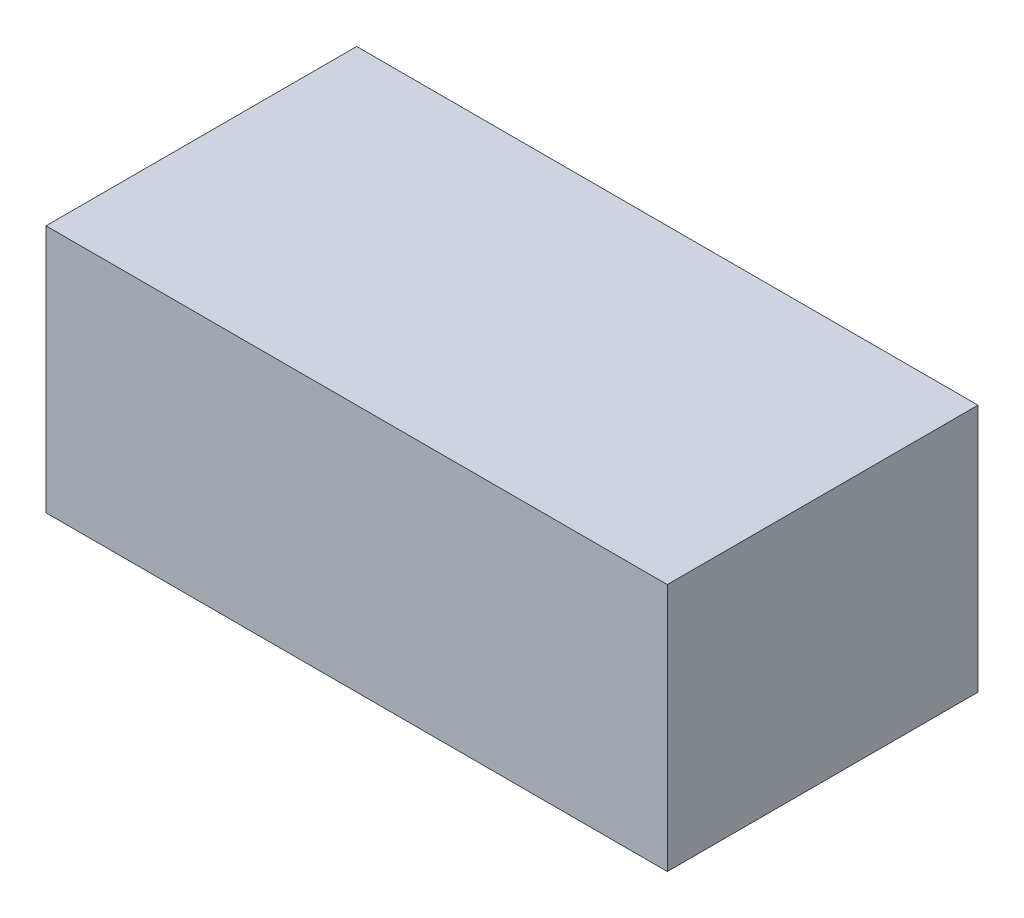
SolidWorks part; units mm, degrees
ref_plane "Front Plane" through (0, 0, 0) normal (0, 0, 1) x (1, 0, 0)
ref_plane "Top Plane" through (0, 0, 0) normal (0, 1, 0) x (1, 0, 0)
ref_plane "Right Plane" through (0, 0, 0) normal (1, 0, 0) x (0, 0, -1)
sketch "Sketch1" plane through (0, 0, 0) normal (0, 1, 0) x (1, 0, 0)
  line L1 (0, 0) -> (20, 0)
  line L2 (0, 0) -> (0, 10)
  line L3 (0, 10) -> (20, 10)
  line L4 (20, 0) -> (20, 10)
  dimension "D1" = 10
  dimension "D2" = 20
extrude "Boss-Extrude1" add sketch "Sketch1" along normal blind 8
